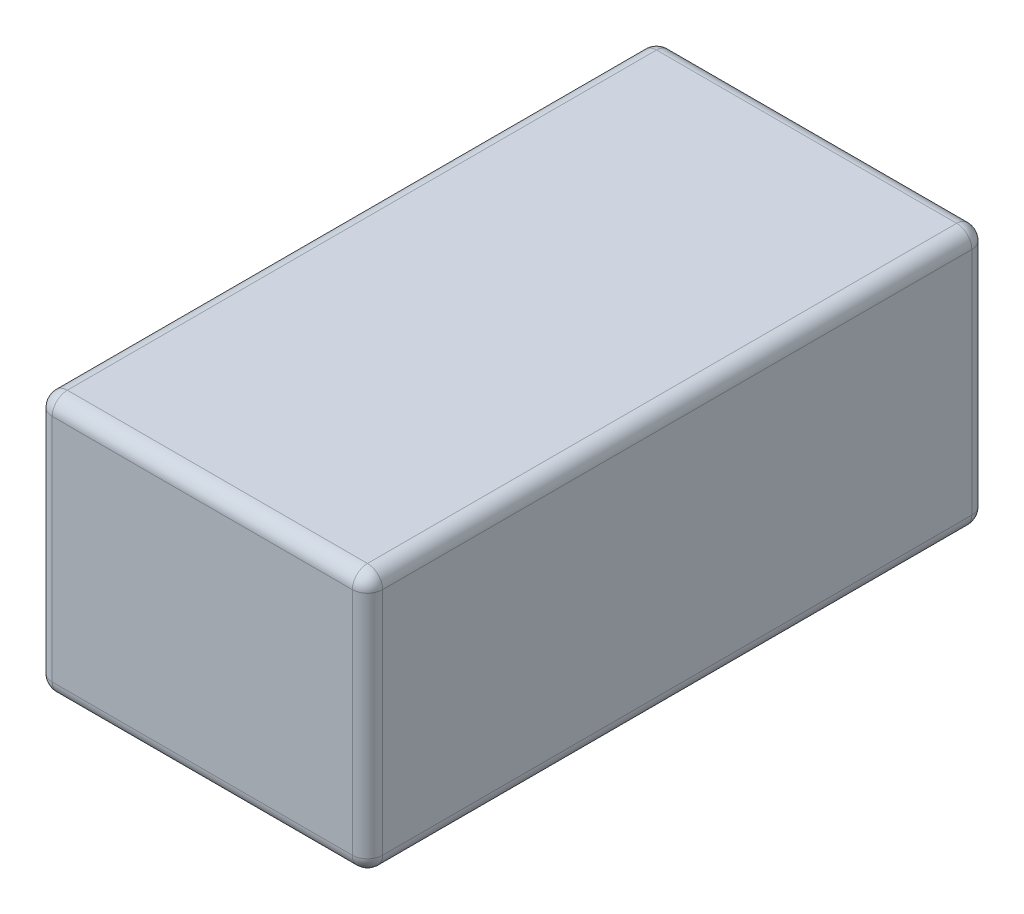
SolidWorks part; units mm, degrees
material "ABS"
ref_plane "Front Plane" through (0, 0, 0) normal (0, 0, 1) x (1, 0, 0)
ref_plane "Top Plane" through (0, 0, 0) normal (0, 1, 0) x (1, 0, 0)
ref_plane "Right Plane" through (0, 0, 0) normal (1, 0, 0) x (0, 0, -1)
sketch "Sketch1" plane through (0, 0, 0) normal (0, 1, 0) x (1, 0, 0)
  line L1 (-41.5925, -77.978) -> (41.5925, -77.978)
  line L2 (-41.5925, -77.978) -> (-41.5925, 77.978)
  line L3 (-41.5925, 77.978) -> (41.5925, 77.978)
  line L4 (41.5925, -77.978) -> (41.5925, 77.978)
  line L5 (-41.5925, -77.978) -> (41.5925, 77.978) construction
  line L6 (-41.5925, 77.978) -> (41.5925, -77.978) construction
  point P0 (0, 0)
  dimension "D1" = 83.185
  dimension "D2" = 155.956
extrude "Boss-Extrude1" add sketch "Sketch1" along normal blind 65.532
fillet "Fillet1" radius 3.81 12 edges at (-41.5925, 0, 0) (41.5925, 0, 0) (41.5925, 32.766, -77.978) (0, 65.532, -77.978) (-41.5925, 32.766, -77.978) (0, 0, -77.978) (-41.5925, 32.766, 77.978) (0, 65.532, 77.978) (41.5925, 32.766, 77.978) (0, 0, 77.978) (41.5925, 65.532, 0) (-41.5925, 65.532, 0)
